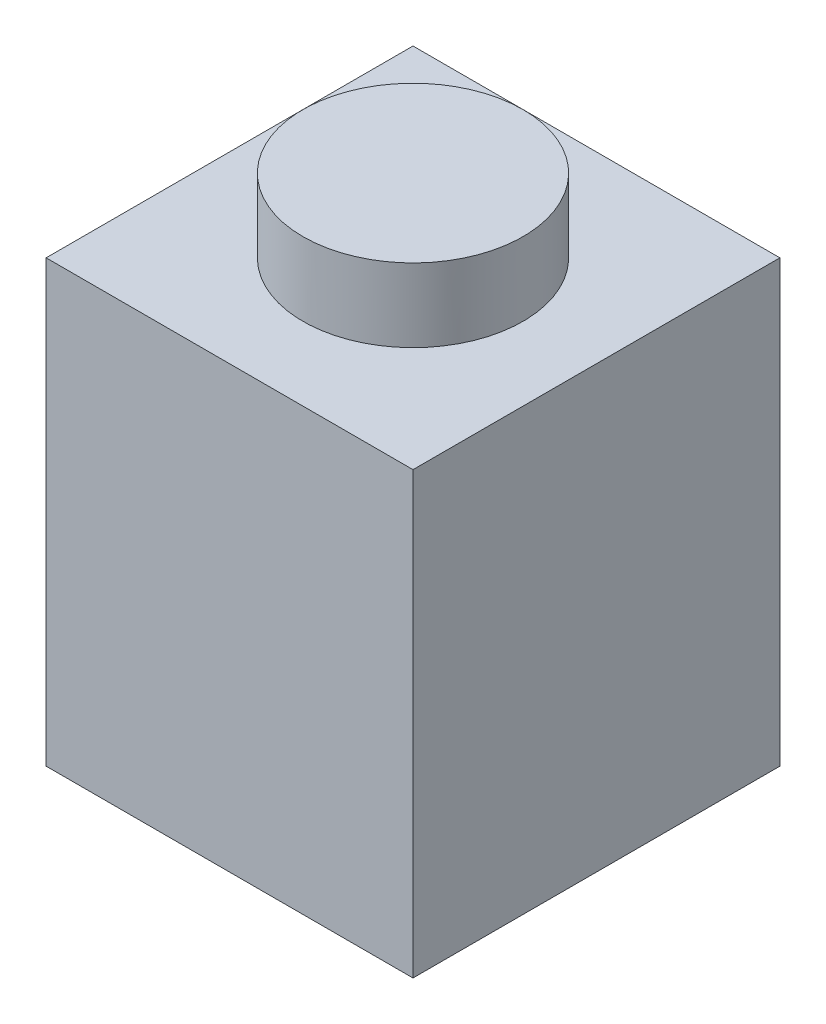
SolidWorks part; units mm, degrees
ref_plane "Front Plane" through (0, 0, 0) normal (0, 0, 1) x (1, 0, 0)
ref_plane "Top Plane" through (0, 0, 0) normal (0, 1, 0) x (1, 0, 0)
ref_plane "Right Plane" through (0, 0, 0) normal (1, 0, 0) x (0, 0, -1)
sketch "Sketch3" plane through (0, 0, 0) normal (0, 1, 0) x (1, 0, 0)
  line L1 (0, 0) -> (8, 0)
  line L2 (0, 0) -> (0, 8)
  line L3 (0, 8) -> (8, 8)
  line L4 (8, 0) -> (8, 8)
  dimension "D1" = 8
  dimension "D2" = 8
extrude "Boss-Extrude1" add sketch "Sketch3" along normal blind 9.6
sketch "Sketch4" plane through (0, 9.6, 0) normal (0, 1, 0) x (1, 0, 0)
  line L0 (0, 8) -> (0, 0) construction
  line L1 (8, 8) -> (0, 8) construction
  circle A0 centre (4, 4) radius 2.4
  dimension "D1" = 4.8
  dimension "D2" = 1.6
  dimension "D3" = 1.6
extrude "Boss-Extrude2" add sketch "Sketch4" along normal blind 1.6
shell "Shell1" thickness 1.8
